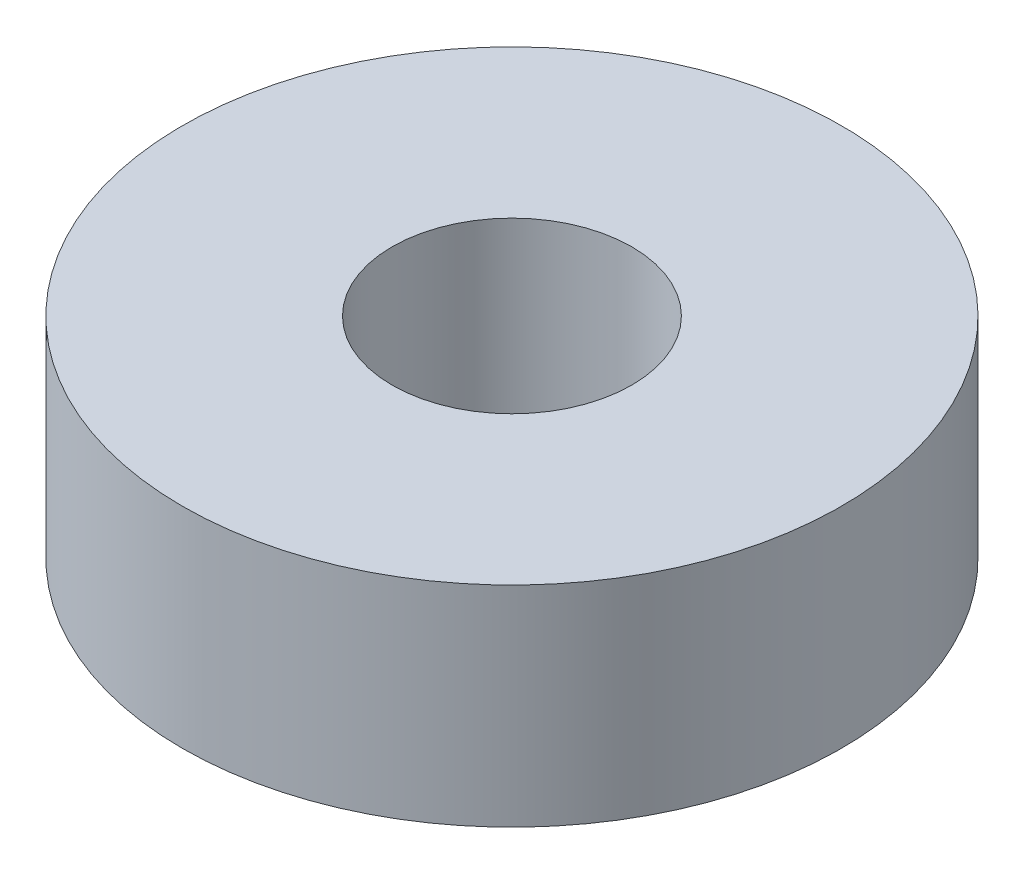
SolidWorks part; units mm, degrees
ref_plane "Front Plane" through (0, 0, 0) normal (0, 0, 1) x (1, 0, 0)
ref_plane "Top Plane" through (0, 0, 0) normal (0, 1, 0) x (1, 0, 0)
ref_plane "Right Plane" through (0, 0, 0) normal (1, 0, 0) x (0, 0, -1)
other "Bounding Box"
ref_plane "Default Plane" through (-8.9266, -12.7485, 0) normal (-0.1736, 0.9848, 0) x (0.9848, 0.1736, 0)
sketch "Sketch1" plane through (0, 0, 0) normal (0, 1, 0) x (1, 0, 0)
  circle A0 centre (0, 0) radius 4
  circle A1 centre (0, 0) radius 11
  dimension "D1" = 8
  dimension "D2" = 22
extrude "Boss-Extrude1" add sketch "Sketch1" along normal mid plane 7
